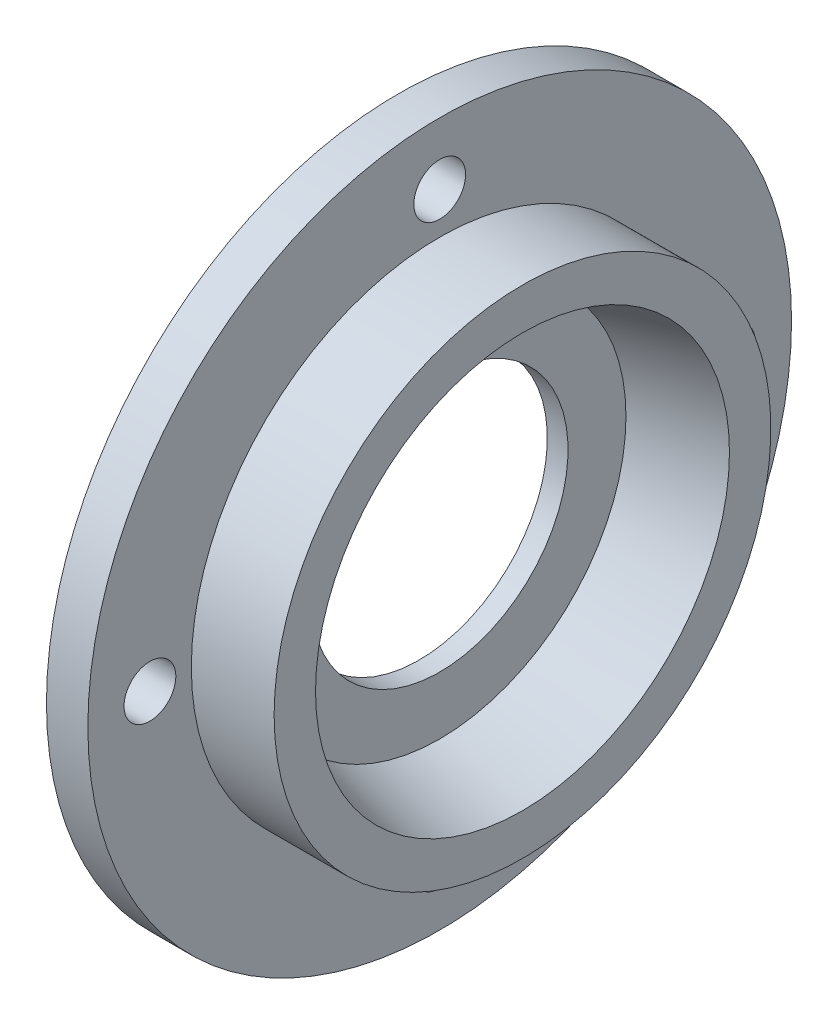
SolidWorks part; units mm, degrees
material "Alloy Steel (SS)"
ref_plane "Front Plane" through (0, 0, 0) normal (0, 0, 1) x (1, 0, 0)
ref_plane "Top Plane" through (0, 0, 0) normal (0, 1, 0) x (1, 0, 0)
ref_plane "Right Plane" through (0, 0, 0) normal (1, 0, 0) x (0, 0, -1)
sketch "Sketch1" plane through (0, 0, 0) normal (0, 0, 1) x (1, 0, 0)
  line L0 (0, 0) -> (24.9927, 0) construction
  line L1 (0, 0) -> (0, 17)
  line L2 (0, 17) -> (2, 17)
  line L3 (2, 17) -> (2, 12)
  line L4 (2, 12) -> (6, 12)
  line L5 (6, 12) -> (6, 10)
  line L7 (2, 9) -> (2, 0)
  line L8 (2, 0) -> (0, 0)
  line L9 (6, 10) -> (2, 9)
  point P5 (6, 11)
  dimension "D1" = 12
  dimension "D2" = 10
  dimension "D3" = 17
  dimension "D4" = 9
  dimension "2" = 2
  dimension "D5" = 4
revolve "Revolve1" add sketch "Sketch1" angle 360 about L0
sketch "Sketch2" plane through (0, 0, 0) normal (-1, 0, 0) x (0, 0, 1)
  circle A0 centre (0, 0) radius 12
  circle A2 centre (0, 0) radius 17 construction
  dimension "D1" = 5
sketch "Sketch4" plane through (0, 0, 0) normal (-1, 0, 0) x (0, 0, 1)
  circle A0 centre (0, 0) radius 14 construction
  circle A1 centre (0, 14) radius 1.25
  circle A2 centre (14, 0) radius 1.25
  circle A3 centre (0, -14) radius 1.25
  circle A4 centre (-14, 0) radius 1.25
  circle A5 centre (0, 0) radius 17 construction
  dimension "D1" = 3
  dimension "D2" = 2.5
extrude "Cut-Extrude3" cut sketch "Sketch4" against normal up to next
extrude "Cut-Extrude4" cut sketch "Sketch2" against normal blind 1
sketch "Sketch5" plane through (1, 0, 0) normal (-1, 0, 0) x (0, 0, 1)
  circle A0 centre (0, 0) radius 6.2
  dimension "D1" = 12.4
extrude "Cut-Extrude5" cut sketch "Sketch5" against normal up to next
